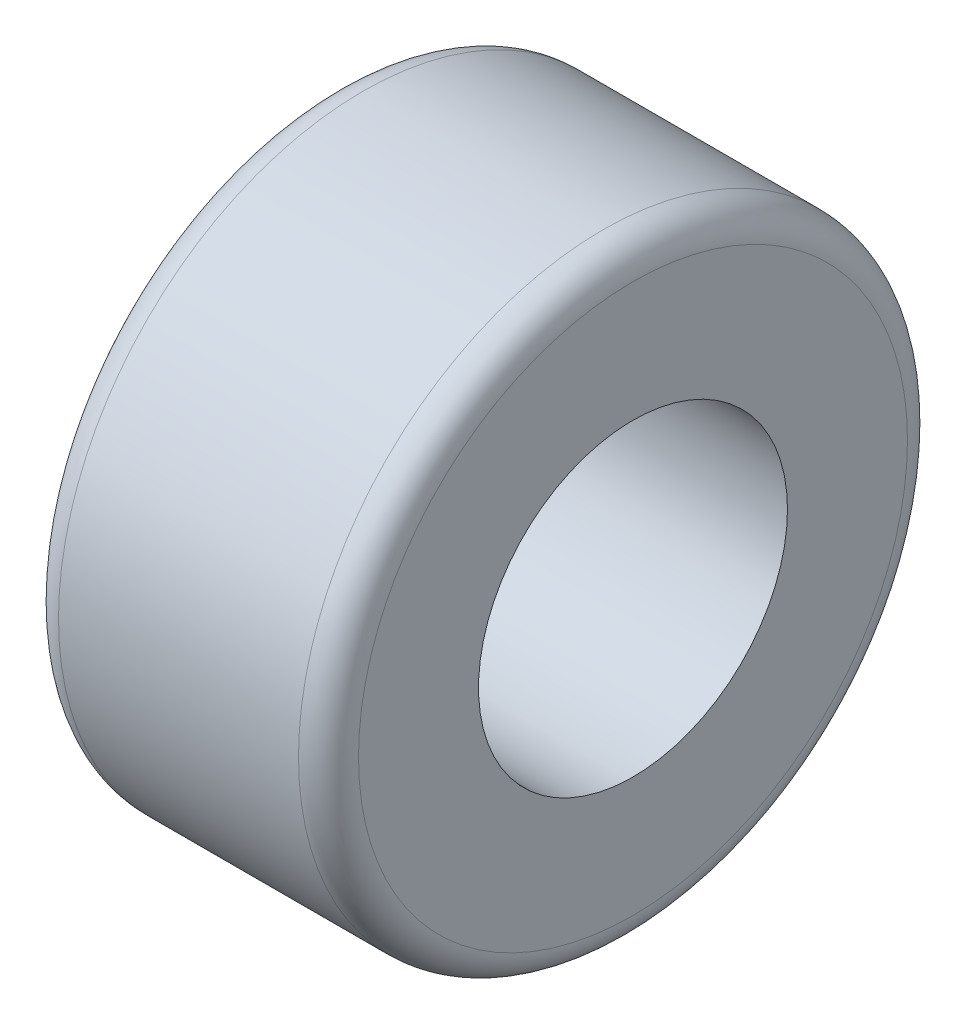
SolidWorks part; units mm, degrees
ref_plane "Front Plane" through (0, 0, 0) normal (0, 0, 1) x (1, 0, 0)
ref_plane "Top Plane" through (0, 0, 0) normal (0, 1, 0) x (1, 0, 0)
ref_plane "Right Plane" through (0, 0, 0) normal (1, 0, 0) x (0, 0, -1)
sketch "Sketch1" plane through (0, 0, 0) normal (1, 0, 0) x (0, 0, -1)
  circle A0 centre (0, 0) radius 5.15
  circle A1 centre (0, 0) radius 10.15
  dimension "D1" = 10.3
  dimension "D2" = 5
extrude "Boss-Extrude1" add sketch "Sketch1" along normal blind 10
fillet "Fillet1" radius 1 2 edges at (0, 0, -10.15) (10, 0, -10.15)
